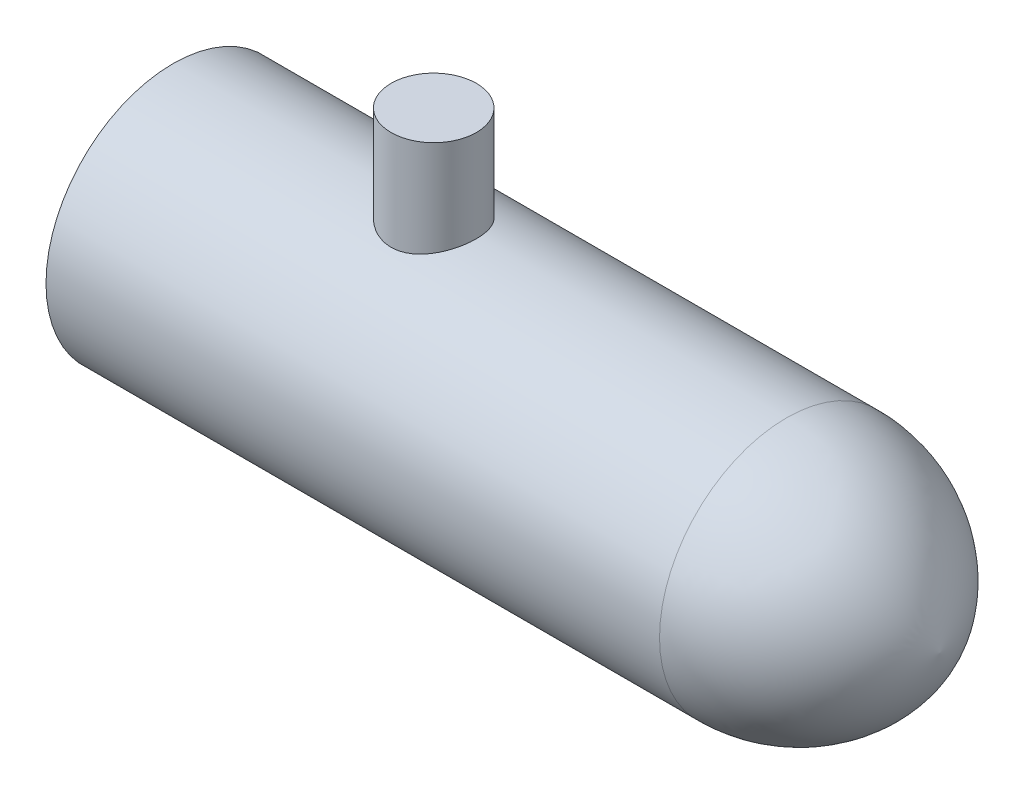
SolidWorks part; units mm, degrees
ref_plane "Front Plane" through (0, 0, 0) normal (0, 0, 1) x (1, 0, 0)
ref_plane "Top Plane" through (0, 0, 0) normal (0, 1, 0) x (1, 0, 0)
ref_plane "Right Plane" through (0, 0, 0) normal (1, 0, 0) x (0, 0, -1)
sketch "Sketch1" plane through (0, 0, 0) normal (1, 0, 0) x (0, 0, -1)
  circle A0 centre (0, 0) radius 52.5526
  dimension "D1" = 105.1052
extrude "Boss-Extrude1" add sketch "Sketch1" along normal mid plane 254
sketch "Sketch2" plane through (0, 0, 0) normal (0, 0, 1) x (1, 0, 0)
  line L0 (127, 52.5526) -> (127, 0)
  line L1 (127, -52.5526) -> (127, 52.5526) construction
  line L2 (127, 0) -> (190.5, 0)
  arc A0 (127, 52.5526) -> (190.5, 0) centre (127, -12.0876) cw
  dimension "D1" = 63.5
revolve "Revolve1" add sketch "Sketch2" angle 360 about L2
ref_plane "Plane1" through (0, 52.5526, 0) normal (0, 1, 0) x (1, 0, 0)
sketch "Sketch4" plane through (0, 52.5526, 0) normal (0, 1, 0) x (1, 0, 0)
  line L0 (-127, 52.5526) -> (-127, -52.5526) construction
  circle A0 centre (-19.05, 0) radius 17.653
  dimension "D1" = 35.306
  dimension "D2" = 107.95
extrude "Boss-Extrude2" add sketch "Sketch4" along normal blind 38.1 and the other way up to next
